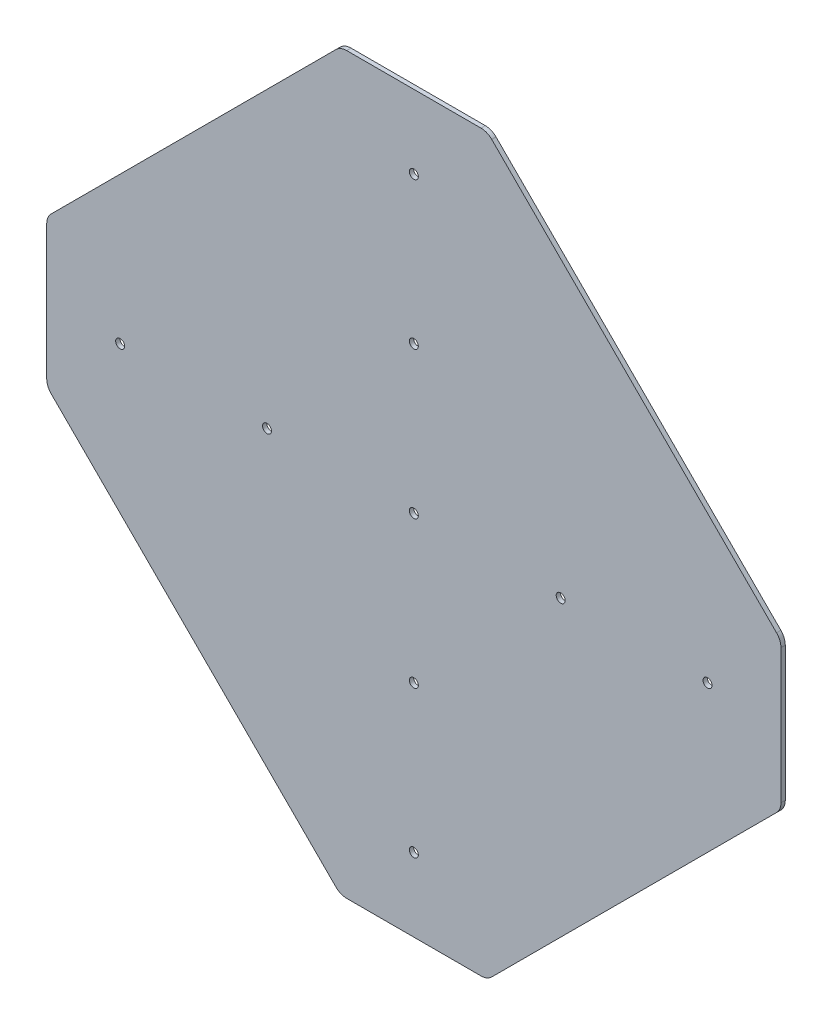
SolidWorks part; units mm, degrees
ref_plane "Front Plane" through (0, 0, 0) normal (0, 0, 1) x (1, 0, 0)
ref_plane "Top Plane" through (0, 0, 0) normal (0, 1, 0) x (1, 0, 0)
ref_plane "Right Plane" through (0, 0, 0) normal (1, 0, 0) x (0, 0, -1)
ref_plane "Plane1" through (0, 0, 0) normal (0, 0, -1) x (-1, 0, 0)
sketch "Sketch1" plane through (0, 0, 0) normal (0, 0, -1) x (-1, 0, 0)
  line L0 (-133.3101, -28.6149) -> (-28.6149, -133.3101)
  line L1 (-24.686, -134.9375) -> (24.686, -134.9375)
  line L2 (28.6149, -133.3101) -> (133.3101, -28.6149)
  line L3 (134.9375, -24.686) -> (134.9375, 24.686)
  line L4 (133.3101, 28.6149) -> (28.6149, 133.3101)
  line L5 (24.686, 134.9375) -> (-24.686, 134.9375)
  line L6 (-28.6149, 133.3101) -> (-133.3101, 28.6149)
  line L7 (-134.9375, 24.686) -> (-134.9375, -24.686)
  circle A0 centre (0, 53.975) radius 1.651
  circle A1 centre (0, 0) radius 1.651
  circle A2 centre (0, -107.95) radius 1.651
  circle A3 centre (0, 107.95) radius 1.651
  circle A4 centre (-53.975, 0) radius 1.651
  circle A5 centre (53.975, 0) radius 1.651
  circle A6 centre (0, -53.975) radius 1.651
  circle A7 centre (-107.95, 0) radius 1.651
  circle A8 centre (107.95, 0) radius 1.651
  arc A9 (-28.6149, -133.3101) -> (-24.686, -134.9375) centre (-24.686, -129.3813) ccw
  arc A10 (24.686, -134.9375) -> (28.6149, -133.3101) centre (24.686, -129.3812) ccw
  arc A11 (133.3101, -28.6149) -> (134.9375, -24.686) centre (129.3813, -24.686) ccw
  arc A12 (134.9375, 24.686) -> (133.3101, 28.6149) centre (129.3813, 24.686) ccw
  arc A13 (28.6149, 133.3101) -> (24.686, 134.9375) centre (24.686, 129.3813) ccw
  arc A14 (-24.686, 134.9375) -> (-28.6149, 133.3101) centre (-24.686, 129.3812) ccw
  arc A15 (-133.3101, 28.6149) -> (-134.9375, 24.686) centre (-129.3812, 24.686) ccw
  arc A16 (-134.9375, -24.686) -> (-133.3101, -28.6149) centre (-129.3812, -24.686) ccw
extrude "Boss-Extrude1" add sketch "Sketch1" against normal blind 1.5875
